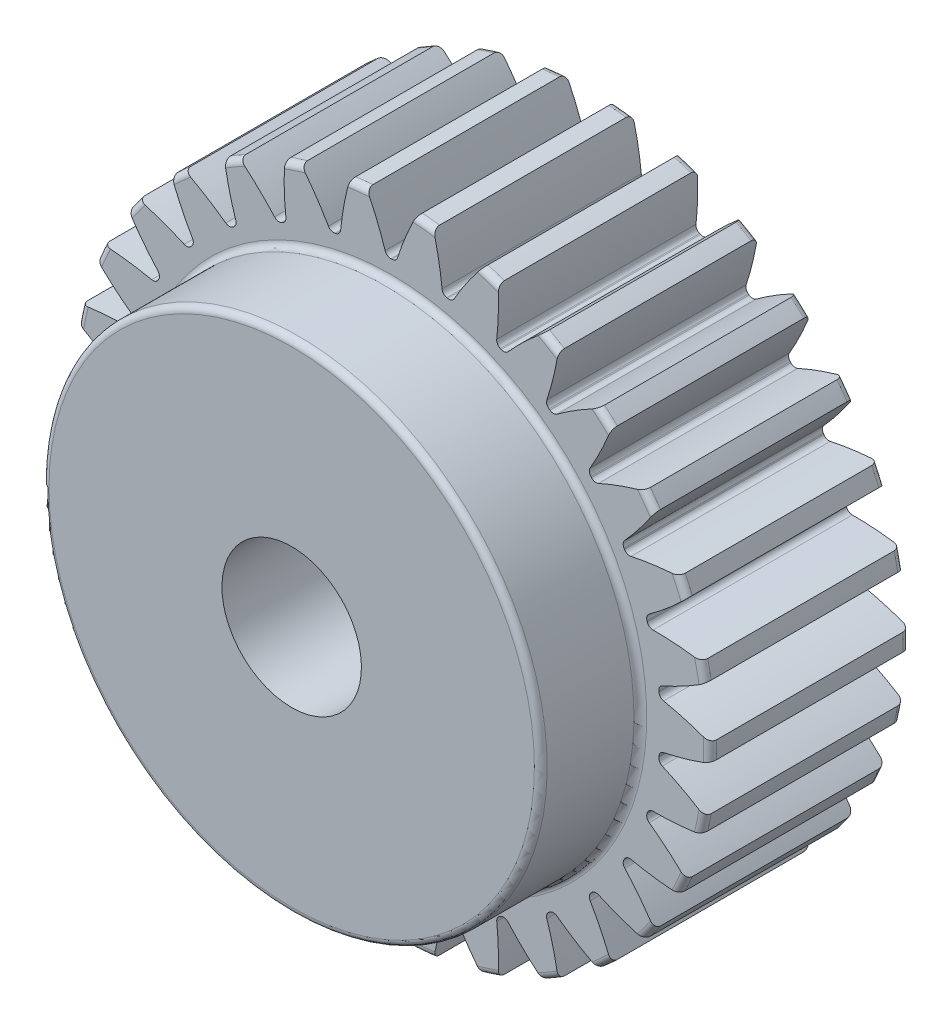
SolidWorks part; units mm, degrees
ref_plane "Front Plane" through (0, 0, 0) normal (0, 0, 1) x (1, 0, 0)
ref_plane "Top Plane" through (0, 0, 0) normal (0, 1, 0) x (1, 0, 0)
ref_plane "Right Plane" through (0, 0, 0) normal (1, 0, 0) x (0, 0, -1)
sketch "Sketch1" plane through (0, 0, 0) normal (0, 0, 1) x (1, 0, 0)
  line L0 (-381, 0) -> (381, 0) construction
  line L1 (0, 0) -> (0, 6) construction
  line L2 (-2, 5.6569) -> (-2, 7.8) construction
  line L3 (-2, 7.8) -> (2, 7.8) construction
  line L4 (2, 7.8) -> (2, 5.6569) construction
  line L5 (0, 6) -> (0, 7.8) construction
  circle A0 centre (0, 0) radius 32 construction
  circle A1 centre (0, 0) radius 30 construction
  circle A2 centre (0, 0) radius 27 construction
  circle A3 centre (0, 0) radius 25 construction
  circle A4 centre (0, 0) radius 6 construction
  dimension "D2" = 2
  dimension "D3" = 5
  dimension "D1" = 5
sketch "Sketch2" plane through (0, 0, 0) normal (1, 0, 0) x (0, 0, -1)
  line L0 (0, 0) -> (-20, 0) construction
  line L1 (-20, 0) -> (-30, 0) construction
  circle A0 centre (-25, 0) radius 2.5
  circle A1 centre (-25, 0) radius 0.4
  dimension "Set Screw Dia" = 5
  dimension "Set Screw Pitch" = 0.8
  dimension "Overall Width" = 30
  dimension "Face Width" = 20
sketch "Sketch4" plane through (0, 0, 0) normal (1, 0, 0) x (0, 0, -1)
  line L0 (-30, 6) -> (-30, 25)
  line L1 (-30, 25) -> (-20, 25)
  line L2 (-20, 25) -> (-20, 32)
  line L3 (-20, 32) -> (0, 32)
  line L4 (0, 32) -> (0, 6)
  line L5 (-20, 25) -> (-20, 0) construction
  line L6 (0, 32) -> (0, -32) construction
  line L7 (-20, 25) -> (0, 25) construction
  line L12 (-30, 6) -> (0, 6)
revolve "Revolve1" add sketch "Sketch4" angle 360 about L1
fillet "Fillet2" radius 0.64 4 edges at (0, 25, 30) (0, 25, 20) (0, 32, 20) (0, 32, 0)
sketch "Sketch7" plane through (0, 0, 20) normal (0, 0, 1) x (1, 0, 0)
  line L0 (0, 0) -> (0, 32) construction
  line L1 (1.5701, 29.9589) -> (2.3983, 31.91) construction
  line L3 (3.3449, 31.8247) -> (3.1359, 29.8357) construction
  line L4 (3.1359, 29.8357) -> (2.8223, 26.8521) construction
  line L5 (0, 0) -> (2.8223, 26.8521) construction
  line L6 (1.5701, 29.9589) -> (0, 0) construction
  line L7 (1.5701, 29.9589) -> (1.6747, 31.9561) construction
  line L8 (1.5701, 29.9589) -> (0, 0) construction
  circle A0 centre (0, 0) radius 32 construction
  arc A1 (-0.0517, 27) -> (0.0517, 27) centre (0, 0) cw
  circle A2 centre (0, 0) radius 27 construction
  arc A3 (-1.5701, 29.9589) -> (1.5701, 29.9589) centre (0, 0) cw construction
  circle A4 centre (0, 0) radius 30 construction
  arc A5 (4.2082, 31.7221) -> (2.4791, 31.9038) centre (0, 0) ccw construction
  arc A6 (1.5701, 29.9589) -> (4.693, 29.6307) centre (0, 0) cw construction
  arc A7 (-2.4791, 31.9038) -> (2.4791, 31.9038) centre (0, 0) cw
  arc A8 (0.6241, 27.4164) -> (2.4791, 31.9038) centre (29.1852, 18.237) cw
  arc A9 (-0.6241, 27.4164) -> (-2.4791, 31.9038) centre (-29.1852, 18.237) ccw
  arc A10 (-0.0517, 27) -> (-0.6241, 27.4164) centre (-0.0528, 27.6) cw
  arc A11 (0.0517, 27) -> (0.6241, 27.4164) centre (0.0528, 27.6) ccw
  point P26 (-0.4922, 26.9955)
  point P29 (0.4922, 26.9955)
  dimension "D4" = 0.6
  dimension "D5" = 30
  dimension "D3" = 20
  dimension "D1" = 6.2832
  dimension "D2" = 3.1416
extrude "Cut-Extrude2" cut sketch "Sketch7" against normal through all
pattern_circular "CirPattern1" count 30 over 360 about axis through (0, 0, 0) along (0, 0, 1) of "Cut-Extrude2"
sketch "Sketch8" plane through (0, 0, 30) normal (0, 0, 1) x (1, 0, 0)
  circle A0 centre (0, 0) radius 7
  dimension "D1" = 14
extrude "Cut-Extrude3" cut sketch "Sketch8" against normal through all both and the other way through all
equation "\"D1@Sketch1\"=2.5*(\"Pitch Dia.@Sketch1\"/\"Number of Teeth@Sketch1\")"
equation "\"D1@CirPattern1\"=\"Number of Teeth@Sketch1\""
equation "\"D1@Fillet2\"=\"OD@Sketch1\"*.01"
equation "\"D1@Sketch7\"=3.14159*(\"Pitch Dia.@Sketch1\"/\"Number of Teeth@Sketch1\")"
equation "\"D2@Sketch7\"=\"D1@Sketch7\"/2"
equation "\"D4@Sketch7\"=\"D1@Sketch7\"*.0955"
equation "\"D5@Sketch7\"=\"Pitch Dia.@Sketch1\"/2"
